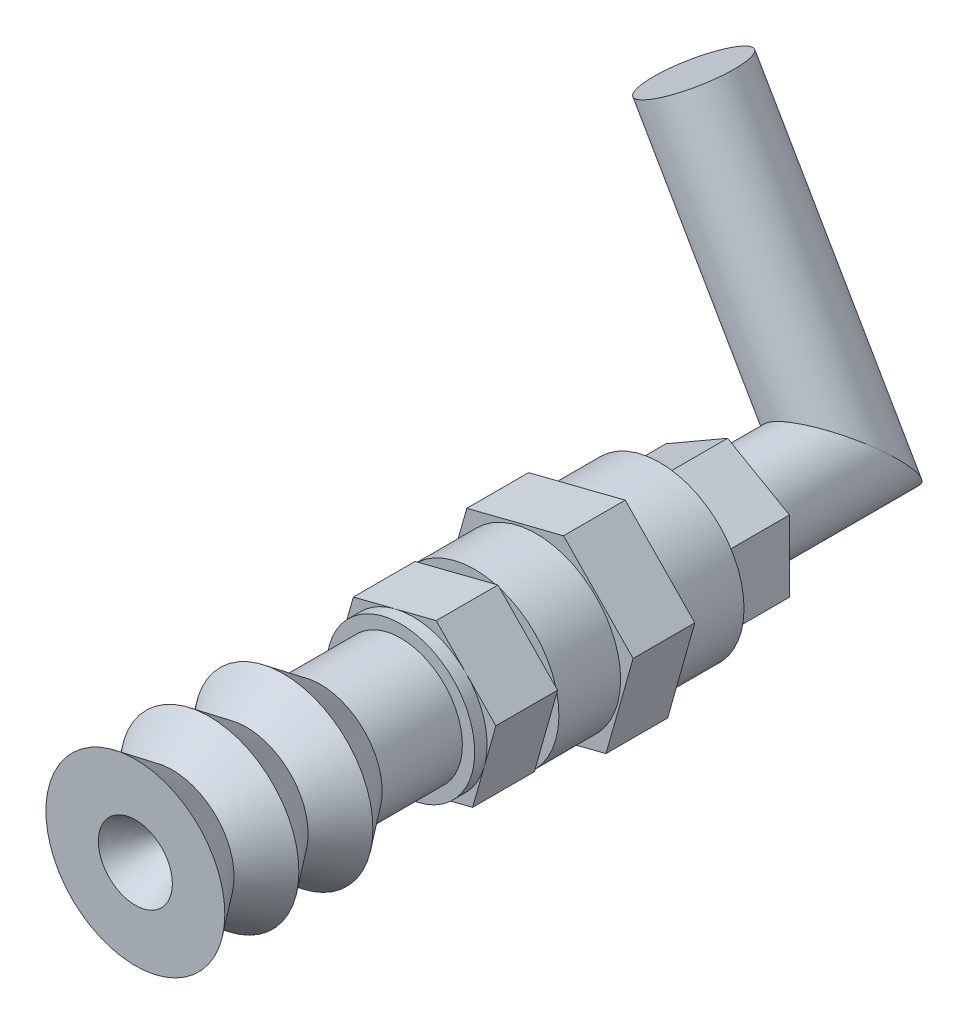
SolidWorks part; units mm, degrees
ref_plane "Plan de face" through (0, 0, 0) normal (0, 0, 1) x (1, 0, 0)
ref_plane "Plan de dessus" through (0, 0, 0) normal (0, 1, 0) x (1, 0, 0)
ref_plane "Plan de droite" through (0, 0, 0) normal (1, 0, 0) x (0, 0, -1)
sketch "Esquisse1" plane through (0, 0, 0) normal (0, 0, 1) x (1, 0, 0)
  circle A0 centre (0, 0) radius 6.825
extrude "Boss.-Extru.1" add sketch "Esquisse1" along normal blind 5
sketch "Esquisse2" plane through (0, 0, 5) normal (0, 0, 1) x (1, 0, 0)
  line L1 (2.1971, 7.7786) -> (-5.6379, 5.7921)
  line L2 (-5.6379, 5.7921) -> (-7.835, -1.9865)
  line L3 (-7.835, -1.9865) -> (-2.1971, -7.7786)
  line L4 (-2.1971, -7.7786) -> (5.6379, -5.7921)
  line L5 (5.6379, -5.7921) -> (7.835, 1.9865)
  line L6 (7.835, 1.9865) -> (2.1971, 7.7786)
  circle A0 centre (0, 0) radius 7 construction
extrude "Boss.-Extru.2" add sketch "Esquisse2" along normal blind 5
sketch "Esquisse3" plane through (0, 0, 10) normal (0, 0, 1) x (1, 0, 0)
  circle A0 centre (0, 0) radius 6.825
  circle A1 centre (0, 0) radius 6.825 construction
extrude "Boss.-Extru.3" add sketch "Esquisse3" along normal blind 5
sketch "Esquisse4" plane through (0, 0, 15) normal (0, 0, 1) x (1, 0, 0)
  line L0 (2.1971, 7.7786) -> (-5.6379, 5.7921) construction
  line L1 (1.8833, 6.6673) -> (-4.8324, 4.9646)
  line L2 (-4.8324, 4.9646) -> (-6.7157, -1.7027)
  line L3 (-6.7157, -1.7027) -> (-1.8833, -6.6673)
  line L4 (-1.8833, -6.6673) -> (4.8324, -4.9646)
  line L5 (4.8324, -4.9646) -> (6.7157, 1.7027)
  line L6 (6.7157, 1.7027) -> (1.8833, 6.6673)
  circle A0 centre (0, 0) radius 6 construction
extrude "Boss.-Extru.4" add sketch "Esquisse4" along normal blind 5
sketch "Esquisse5" plane through (0, 0, 20) normal (0, 0, 1) x (1, 0, 0)
  circle A0 centre (0, 0) radius 6
extrude "Boss.-Extru.5" add sketch "Esquisse5" along normal blind 1
ref_plane "Plan1" through (0, 0, 0) normal (-0.9623, 0.2718, 0) x (0, 0, 1)
sketch "Esquisse6" plane through (0, 0, 0) normal (-0.9623, 0.2718, 0) x (0, 0, 1)
  line L0 (42.5, 7.25) -> (42.5, 3)
  line L1 (20, 0) -> (20, -3.4641) construction
  line L2 (38.0005, 0) -> (20, 0)
  line L3 (20, 0) -> (20, 5)
  line L4 (20, 5) -> (27.5, 5)
  line L5 (27.5, 5) -> (30.5, 7.25)
  line L6 (30.5, 7.25) -> (33.5, 5)
  line L7 (33.5, 5) -> (36.5, 7.25)
  line L8 (36.5, 7.25) -> (39.5, 5)
  line L9 (39.5, 5) -> (42.5, 7.25)
  line L10 (42.5, 7.25) -> (24.829, 7.25) construction
  arc A1 (42.5, 3) -> (38.0005, 0) centre (53.5911, -18.509) ccw
  point P12 (42.5, 5.4149)
  point P14 (24.8554, 7.25)
  point P15 (24.829, 7.25)
  point P18 (42.5, 7.25)
  dimension "D3" = 5
  dimension "D4" = 7.5
  dimension "D1" = 22.5
  dimension "D2" = 7.25
  dimension "D5" = 4.25
sketch "Esquisse7" plane through (0, 0, 0) normal (-0.9623, 0.2718, 0) x (0, 0, 1)
  line L0 (27.4292, 0) -> (-2.7103, 0) construction
revolve "Révolution1" add sketch "Esquisse6" angle 360 about L0
ref_plane "Plan2" through (0, 0, 20) normal (0, 0, -1) x (-1, 0, 0)
sketch "Esquisse8" plane through (0, 0, 20) normal (0, 0, -1) x (-1, 0, 0)
  circle A0 centre (0, 0) radius 4
extrude "Boss.-Extru.6" add sketch "Esquisse8" against normal blind 4
shell "Coque1" [suppressed] thickness 3
sketch "Esquisse10" plane through (0, 0, 0) normal (0, 0, -1) x (-1, 0, 0)
  line L1 (5, -2.8868) -> (5, 2.8868)
  line L2 (5, 2.8868) -> (0, 5.7735)
  line L3 (0, 5.7735) -> (-5, 2.8868)
  line L4 (-5, 2.8868) -> (-5, -2.8868)
  line L5 (-5, -2.8868) -> (0, -5.7735)
  line L6 (0, -5.7735) -> (5, -2.8868)
  circle A0 centre (0, 0) radius 5 construction
extrude "Boss.-Extru.7" add sketch "Esquisse10" along normal blind 5.5
sketch "Esquisse11" plane through (0, 0, -5.5) normal (0, 0, -1) x (-1, 0, 0)
  circle A1 centre (0, 0) radius 3.75
extrude "Boss.-Extru.8" add sketch "Esquisse11" along normal blind 13
sketch "Esquisse15" plane through (-2.5, 4.3301, 0) normal (-0.5, 0.866, 0) x (0.866, 0.5, 0)
  line L0 (3.75, 18.5) -> (-3.75, 18.5) construction
  line L1 (-2.8868, 5.5) -> (2.8868, 5.5) construction
  circle A0 centre (0, 14.75) radius 3.75
  point P7 (0, 5.5)
extrude "Boss.-Extru.9" add sketch "Esquisse15" along normal blind 19 and the other way blind 11
sketch "Esquisse17" plane through (-12, 20.7846, 0) normal (-0.5, 0.866, 0) x (0.866, 0.5, 0)
  line L0 (3.75, 14.75) -> (7.0894, 14.75)
  line L1 (-7.0027, 14.75) -> (-3.75, 14.75)
  line L2 (-7.0027, 14.75) -> (-7.0027, 20.4689)
  line L3 (-7.0027, 20.4689) -> (7.0894, 20.4689)
  line L4 (7.0894, 14.75) -> (7.0894, 20.4689)
  arc A0 (3.75, 14.75) -> (-3.75, 14.75) centre (0, 14.75) ccw
extrude "Enlèv. mat.-Extru.1" cut sketch "Esquisse17" against normal blind 36
sketch "Esquisse18" plane through (0, 0, -5.5) normal (0, 0, -1) x (-1, 0, 0)
  line L0 (14.8926, -8.5982) -> (3.2476, -1.875)
  line L1 (-12.634, 7.2942) -> (-3.4461, -21.4129)
  line L2 (-3.4461, -21.4129) -> (14.8926, -8.5982)
  line L3 (15.2476, 18.9096) -> (8.7524, 22.6596) construction
  line L4 (-3.2476, 1.875) -> (-12.634, 7.2942)
  arc A0 (-3.2476, 1.875) -> (3.2476, -1.875) centre (0, 0) ccw
extrude "Enlèv. mat.-Extru.2" cut sketch "Esquisse18" along normal blind 24
